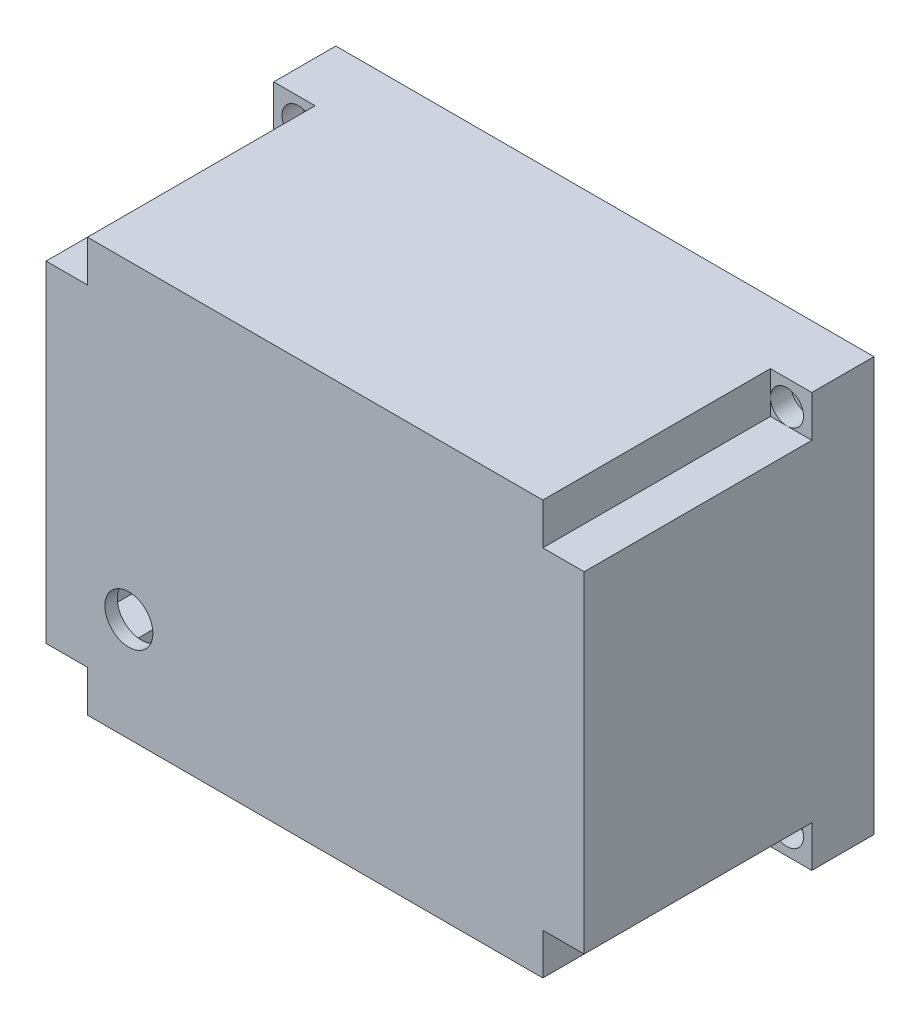
SolidWorks part; units mm, degrees
ref_plane "Front Plane" through (0, 0, 0) normal (0, 0, 1) x (1, 0, 0)
ref_plane "Top Plane" through (0, 0, 0) normal (0, 1, 0) x (1, 0, 0)
ref_plane "Right Plane" through (0, 0, 0) normal (1, 0, 0) x (0, 0, -1)
sketch "Sketch2" plane through (0, 0, 0) normal (0, 1, 0) x (1, 0, 0)
  line L1 (0, 0) -> (130, 0)
  line L2 (0, 0) -> (0, 70)
  line L3 (0, 70) -> (130, 70)
  line L4 (130, 0) -> (130, 70)
  dimension "D1" = 130
  dimension "D2" = 70
extrude "Boss-Extrude1" add sketch "Sketch2" along normal blind 100
sketch "Sketch3" plane through (0, 0, -70) normal (0, 0, -1) x (-1, 0, 0)
  line L0 (-130, 100) -> (0, 100) construction
  line L1 (-117, 87) -> (-13, 87)
  line L2 (-117, 87) -> (-117, 13)
  line L3 (-117, 13) -> (-13, 13)
  line L4 (-13, 87) -> (-13, 13)
  line L5 (-117, 87) -> (-13, 13) construction
  line L6 (-117, 13) -> (-13, 87) construction
  line L7 (-130, 100) -> (-130, 0) construction
  line L8 (-130, 0) -> (0, 0) construction
  line L9 (0, 100) -> (0, 0) construction
  point P0 (-65, 50)
  dimension "D1" = 13
  dimension "D2" = 13
  dimension "D3" = 13
  dimension "D4" = 13
extrude "Cut-Extrude1" cut sketch "Sketch3" against normal blind 67
sketch "Sketch4" plane through (0, 0, 0) normal (0, 0, 1) x (1, 0, 0)
  line L1 (0, 100) -> (10, 100)
  line L2 (0, 100) -> (0, 90)
  line L3 (0, 90) -> (10, 90)
  line L4 (10, 100) -> (10, 90)
  line L5 (130, 100) -> (120, 100)
  line L6 (130, 100) -> (130, 90)
  line L7 (130, 90) -> (120, 90)
  line L8 (120, 100) -> (120, 90)
  line L9 (0, 0) -> (10, 0)
  line L10 (0, 0) -> (0, 10)
  line L11 (0, 10) -> (10, 10)
  line L12 (10, 0) -> (10, 10)
  line L13 (130, 0) -> (120, 0)
  line L14 (130, 0) -> (130, 10)
  line L15 (130, 10) -> (120, 10)
  line L16 (120, 0) -> (120, 10)
  dimension "D1" = 10
  dimension "D2" = 10
  dimension "D3" = 10
  dimension "D4" = 10
  dimension "D5" = 10
  dimension "D6" = 10
  dimension "D7" = 10
  dimension "D8" = 10
extrude "Cut-Extrude2" cut sketch "Sketch4" against normal blind 55
sketch "Sketch5" plane through (0, 0, -70) normal (0, 0, -1) x (-1, 0, 0)
  line L0 (-130, 100) -> (0, 100) construction
  line L1 (-117, 87) -> (-13, 87)
  line L2 (-117, 87) -> (-117, 97)
  line L3 (-117, 97) -> (-13, 97)
  line L4 (-13, 87) -> (-13, 97)
  line L9 (-13, 13) -> (-117, 13)
  line L10 (-13, 13) -> (-13, 3)
  line L11 (-13, 3) -> (-117, 3)
  line L12 (-117, 13) -> (-117, 3)
  line L18 (-130, 0) -> (0, 0) construction
  dimension "D1" = 3
  dimension "D3" = 3
extrude "Cut-Extrude3" cut sketch "Sketch5" against normal blind 67
sketch "Sketch6" plane through (0, 0, -70) normal (0, 0, -1) x (-1, 0, 0)
  line L0 (-117, 97) -> (-117, 3) construction
  line L1 (-117, 87) -> (-127, 87)
  line L2 (-117, 87) -> (-117, 13)
  line L3 (-117, 13) -> (-127, 13)
  line L4 (-127, 87) -> (-127, 13)
  line L5 (-13, 3) -> (-13, 97) construction
  line L6 (-13, 87) -> (-3, 87)
  line L7 (-13, 87) -> (-13, 13)
  line L8 (-13, 13) -> (-3, 13)
  line L9 (-3, 87) -> (-3, 13)
  line L10 (-130, 100) -> (-130, 0) construction
  line L11 (-130, 100) -> (0, 100) construction
  line L12 (-130, 0) -> (0, 0) construction
  line L13 (0, 100) -> (0, 0) construction
  dimension "D1" = 3
  dimension "D2" = 13
  dimension "D3" = 13
  dimension "D4" = 13
  dimension "D5" = 3
  dimension "D6" = 13
extrude "Cut-Extrude4" cut sketch "Sketch6" against normal blind 67
sketch "Sketch9" plane through (0, 0, -70) normal (0, 0, -1) x (-1, 0, 0)
  line L0 (-130, 100) -> (0, 100) construction
  line L1 (-130, 100) -> (-130, 0) construction
  line L2 (0, 100) -> (0, 0) construction
  line L3 (-130, 0) -> (0, 0) construction
  circle A0 centre (-124, 94) radius 1.75
  circle A1 centre (-124, 6) radius 1.75
  circle A2 centre (-6, 94) radius 1.75
  circle A3 centre (-6, 6) radius 1.75
  point P4 (-107.3713, 88.8655)
  point P7 (-7.8416, 92)
  point P8 (-123.9805, 6.1022)
  point P11 (-7.8416, 6.1022)
  point P12 (-122.8257, 93.5015)
  dimension "D1" = 3.5
  dimension "D4" = 3.5
  dimension "D7" = 3.5
  dimension "D10" = 3.5
  dimension "D2" = 6
  dimension "D3" = 6
  dimension "D5" = 6
  dimension "D6" = 6
  dimension "D8" = 6
  dimension "D9" = 6
  dimension "D11" = 6
  dimension "D12" = 6
extrude "Cut-Extrude5" cut sketch "Sketch9" against normal blind 67
sketch "Sketch10" plane through (0, 0, -55) normal (0, 0, 1) x (1, 0, 0)
  line L0 (130, 100) -> (120, 100) construction
  line L1 (130, 90) -> (130, 100) construction
  circle A0 centre (124, 94) radius 4
  dimension "D3" = 8
  dimension "D1" = 6
  dimension "D2" = 6
extrude "Cut-Extrude6" cut sketch "Sketch10" against normal blind 5
sketch "Sketch12" plane through (0, 0, -55) normal (0, 0, 1) x (1, 0, 0)
  line L0 (130, 0) -> (130, 10) construction
  line L1 (120, 0) -> (130, 0) construction
  circle A0 centre (124, 6) radius 4
  dimension "D3" = 8
  dimension "D1" = 6
  dimension "D2" = 6
extrude "Cut-Extrude7" cut sketch "Sketch12" against normal blind 5
sketch "Sketch13" plane through (0, 0, -55) normal (0, 0, 1) x (1, 0, 0)
  line L0 (0, 0) -> (10, 0) construction
  line L1 (0, 10) -> (0, 0) construction
  circle A0 centre (6, 6) radius 4
  dimension "D3" = 8
  dimension "D1" = 6
  dimension "D2" = 6
extrude "Cut-Extrude8" cut sketch "Sketch13" against normal blind 5
sketch "Sketch14" plane through (0, 0, -55) normal (0, 0, 1) x (1, 0, 0)
  line L0 (0, 100) -> (0, 90) construction
  line L1 (10, 100) -> (0, 100) construction
  circle A0 centre (6, 94) radius 4
  dimension "D3" = 8
  dimension "D1" = 6
  dimension "D2" = 6
extrude "Cut-Extrude9" cut sketch "Sketch14" against normal blind 5
sketch "Sketch15" plane through (0, 0, -70) normal (0, 0, -1) x (-1, 0, 0)
  line L1 (-117, 87) -> (-120, 87)
  line L2 (-117, 87) -> (-117, 90)
  line L3 (-117, 90) -> (-120, 90)
  line L4 (-120, 87) -> (-120, 90)
  line L5 (-117, 13) -> (-120, 13)
  line L6 (-117, 13) -> (-117, 10)
  line L7 (-117, 10) -> (-120, 10)
  line L8 (-120, 13) -> (-120, 10)
  line L9 (-13, 13) -> (-10, 13)
  line L10 (-13, 13) -> (-13, 10)
  line L11 (-13, 10) -> (-10, 10)
  line L12 (-10, 13) -> (-10, 10)
  line L13 (-13, 87) -> (-10, 87)
  line L14 (-13, 87) -> (-13, 90)
  line L15 (-13, 90) -> (-10, 90)
  line L16 (-10, 87) -> (-10, 90)
  dimension "D1" = 3
  dimension "D2" = 3
  dimension "D3" = 3
  dimension "D4" = 3
  dimension "D5" = 3
  dimension "D6" = 3
  dimension "D7" = 3
  dimension "D8" = 3
extrude "Boss-Extrude2" add sketch "Sketch15" along normal blind 5
sketch "Sketch16" plane through (0, 3, 0) normal (0, 1, 0) x (1, 0, 0)
  line L3 (117, 70) -> (41, 70)
  line L4 (117, 70) -> (117, 67)
  line L5 (117, 67) -> (41, 67)
  line L6 (41, 70) -> (41, 67)
  dimension "D1" = 3
  dimension "D2" = 76
extrude "Boss-Extrude3" add sketch "Sketch16" along normal blind 15
sketch "Sketch17" plane through (0, 0, -3) normal (0, 0, -1) x (-1, 0, 0)
  line L0 (-117, 18) -> (-41, 18) construction
  line L1 (-101, 18) -> (-98, 18)
  line L2 (-101, 18) -> (-101, 48)
  line L3 (-101, 48) -> (-98, 48)
  line L4 (-98, 18) -> (-98, 48)
  line L5 (-117, 18) -> (-117, 13) construction
  line L6 (-38, 18) -> (-35, 18)
  line L7 (-38, 18) -> (-38, 48)
  line L8 (-38, 48) -> (-35, 48)
  line L9 (-35, 18) -> (-35, 48)
  dimension "D1" = 30
  dimension "D2" = 30
  dimension "D3" = 3
  dimension "D4" = 3
  dimension "D5" = 16
  dimension "D6" = 60
extrude "Boss-Extrude4" add sketch "Sketch17" along normal blind 15
sketch "Sketch18" plane through (0, 0, -3) normal (0, 0, -1) x (-1, 0, 0)
  line L0 (-130, 0) -> (0, 0) construction
  line L1 (0, 100) -> (0, 0) construction
  circle A0 centre (-20, 25) radius 5.8
  dimension "D1" = 11.6
  dimension "D2" = 25
  dimension "D3" = 20
extrude "Cut-Extrude10" cut sketch "Sketch18" against normal blind 15
